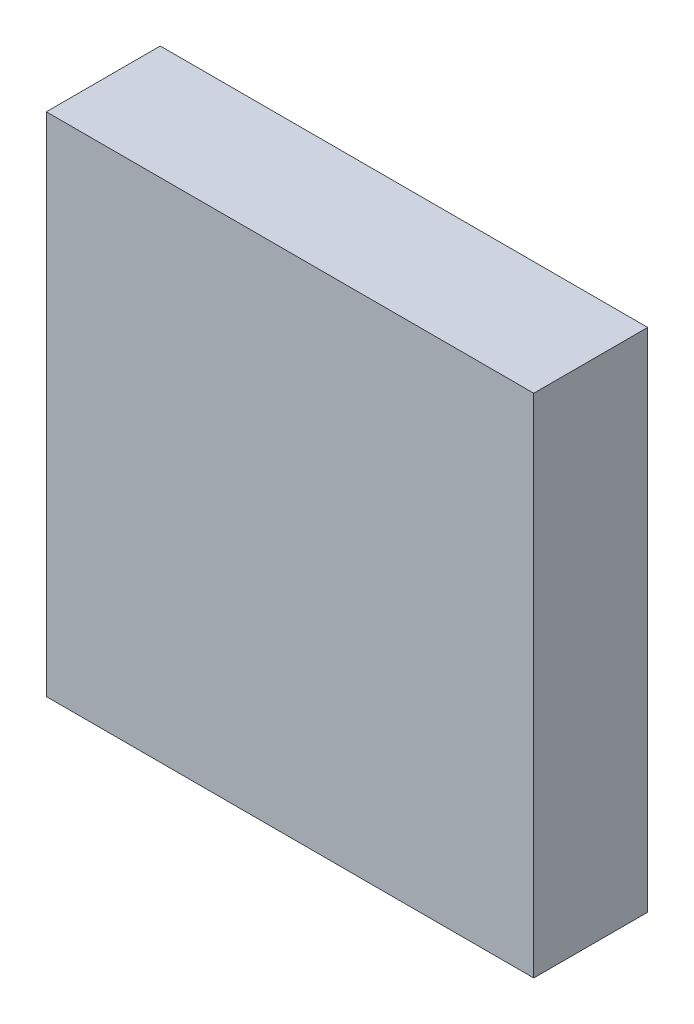
SolidWorks part; units mm, degrees
ref_plane "Front Plane" through (0, 0, 0) normal (0, 0, 1) x (1, 0, 0)
ref_plane "Top Plane" through (0, 0, 0) normal (0, 1, 0) x (1, 0, 0)
ref_plane "Right Plane" through (0, 0, 0) normal (1, 0, 0) x (0, 0, -1)
sketch "Sketch1" plane through (0, 0, 0) normal (0, 0, 1) x (1, 0, 0)
  line L0 (0, 0) -> (8672.5177, 0) construction
  line L1 (0, 0) -> (0, -8672.5177) construction
  line L3 (-19.25, -20) -> (19.25, -20)
  line L4 (-19.25, -20) -> (-19.25, 20)
  line L5 (-19.25, 20) -> (19.25, 20)
  line L6 (19.25, -20) -> (19.25, 20)
  line L7 (-19.25, -20) -> (19.25, 20) construction
  line L8 (-19.25, 20) -> (19.25, -20) construction
  point P5 (0, 0)
  dimension "D1" = 40
  dimension "D2" = 38.5
extrude "Boss-Extrude1" add sketch "Sketch1" along normal mid plane 9
